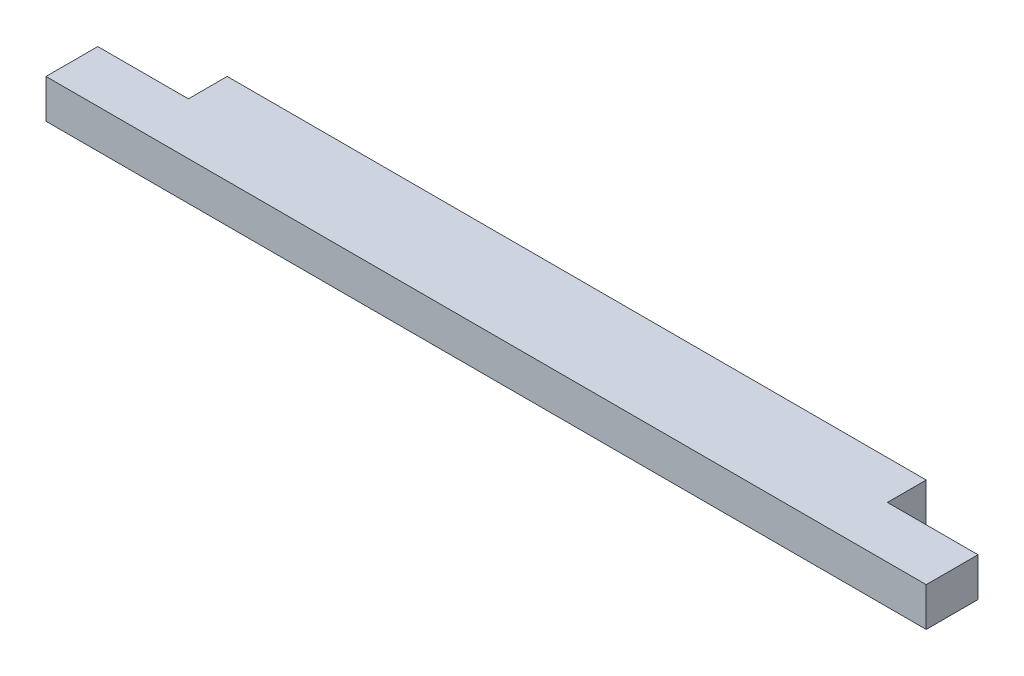
SolidWorks part; units mm, degrees
material "Pine"
ref_plane "Front Plane" through (0, 0, 0) normal (0, 0, 1) x (1, 0, 0)
ref_plane "Top Plane" through (0, 0, 0) normal (0, 1, 0) x (1, 0, 0)
ref_plane "Right Plane" through (0, 0, 0) normal (1, 0, 0) x (0, 0, -1)
sketch "Sketch1" plane through (0, 0, 0) normal (0, 1, 0) x (1, 0, 0)
  line L1 (0, 0) -> (863.6, 0)
  line L2 (0, 0) -> (0, 88.9)
  line L3 (0, 88.9) -> (863.6, 88.9)
  line L4 (863.6, 0) -> (863.6, 88.9)
  dimension "D1" = 88.9
  dimension "D2" = 863.6
extrude "Boss-Extrude1" add sketch "Sketch1" along normal blind 38.1
sketch "Sketch3" plane through (0, 38.1, 0) normal (0, 1, 0) x (1, 0, 0)
  line L1 (0, 88.9) -> (88.9, 88.9)
  line L2 (0, 88.9) -> (0, 50.8)
  line L3 (0, 50.8) -> (88.9, 50.8)
  line L4 (88.9, 88.9) -> (88.9, 50.8)
  line L5 (863.6, 88.9) -> (774.7, 88.9)
  line L6 (863.6, 88.9) -> (863.6, 50.8)
  line L7 (863.6, 50.8) -> (774.7, 50.8)
  line L8 (774.7, 88.9) -> (774.7, 50.8)
  dimension "D1" = 88.9
  dimension "D2" = 88.9
  dimension "D3" = 38.1
  dimension "D4" = 38.1
extrude "Cut-Extrude1" cut sketch "Sketch3" against normal through all
